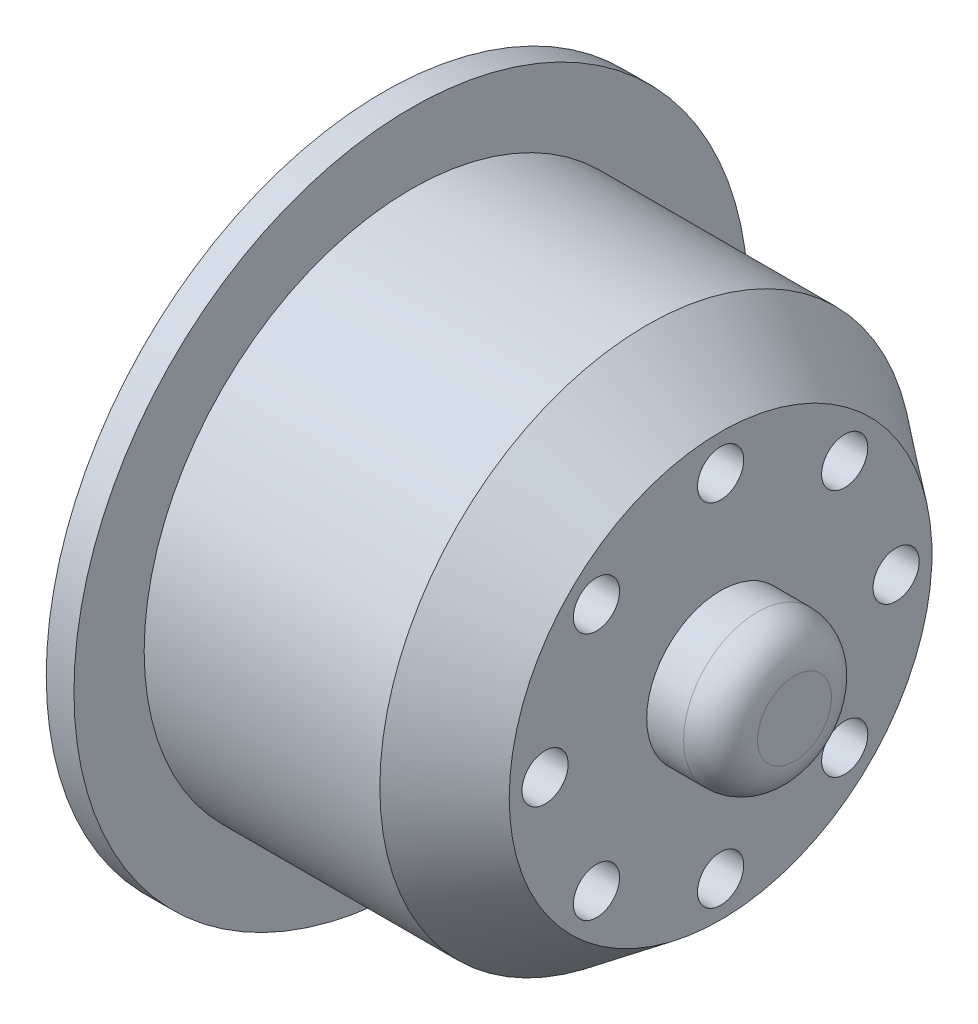
SolidWorks part; units mm, degrees
ref_plane "Front Plane" through (0, 0, 0) normal (0, 0, 1) x (1, 0, 0)
ref_plane "Top Plane" through (0, 0, 0) normal (0, 1, 0) x (1, 0, 0)
ref_plane "Right Plane" through (0, 0, 0) normal (1, 0, 0) x (0, 0, -1)
sketch "Sketch1" plane through (0, 0, 0) normal (0, 1, 0) x (1, 0, 0)
  line L0 (-12.3913, 0) -> (21, 0) construction
  line L1 (-6.1304, 14.45) -> (6.6264, 14.45)
  line L2 (6.6264, 14.45) -> (10.6196, 11.4409)
  line L5 (13.3727, 0) -> (-6.1304, 0)
  line L7 (10.6196, 11.4409) -> (10.6196, 4)
  line L8 (10.6196, 4) -> (14.6196, 4)
  line L9 (14.6196, 4) -> (14.6196, 0)
  line L10 (14.6196, 0) -> (13.3727, 0)
  line L11 (-6.1304, 14.45) -> (-6.1304, 18.25)
  line L12 (-6.1304, 18.25) -> (-7.6304, 18.25)
  line L13 (-7.6304, 18.25) -> (-7.6304, 0)
  line L14 (-7.6304, 0) -> (-6.1304, 0)
  dimension "D1" = 3.9932
  dimension "D2" = 143
  dimension "D3" = 127
  dimension "D4" = 5
  dimension "D5" = 28.9
  dimension "D6" = 16.75
  dimension "D7" = 4
  dimension "D8" = 8
  dimension "D9" = 3.8
  dimension "D10" = 1.5
revolve "Revolve1" add sketch "Sketch1" angle 360 about L0
sketch "Sketch2" plane through (10.6196, 0, 0) normal (1, 0, 0) x (0, 0, -1)
  circle A0 centre (0, 0) radius 9.5 construction
  circle A1 centre (0, 9.5) radius 1.25
  circle A3 centre (6.7175, 6.7175) radius 1.25
  circle A4 centre (9.5, 0) radius 1.25
  circle A5 centre (6.7175, -6.7175) radius 1.25
  circle A6 centre (0, -9.5) radius 1.25
  circle A7 centre (-6.7175, -6.7175) radius 1.25
  circle A8 centre (-9.5, 0) radius 1.25
  circle A9 centre (-6.7175, 6.7175) radius 1.25
  point P22 (0, 0)
  dimension "D1" = 19
  dimension "D2" = 2.5
  dimension "D3" = 8
extrude "Cut-Extrude1" cut sketch "Sketch2" against normal through all
fillet "Fillet1" radius 2 1 edges at (14.6196, 0, 4)
sketch "Sketch3" plane through (-7.6304, 0, 0) normal (-1, 0, 0) x (0, 0, 1)
  circle A0 centre (0, 0) radius 9.5 construction
  circle A1 centre (0, 9.5) radius 2.5
  circle A2 centre (6.7175, 6.7175) radius 2.5
  circle A3 centre (9.5, 0) radius 2.5
  circle A4 centre (6.7175, -6.7175) radius 2.5
  circle A5 centre (0, -9.5) radius 2.5
  circle A6 centre (-6.7175, -6.7175) radius 2.5
  circle A7 centre (-9.5, 0) radius 2.5
  circle A8 centre (-6.7175, 6.7175) radius 2.5
  point P23 (0, 0)
  dimension "D1" = 19
  dimension "D2" = 5
  dimension "D3" = 8
extrude "Cut-Extrude2" cut sketch "Sketch3" against normal offset from surface (13.25 mm away) 5 up to face at (10.6196, 9.5, -1.25)
sketch "Sketch4" plane through (-7.6304, 0, 0) normal (-1, 0, 0) x (0, 0, 1)
  circle A0 centre (0, 0) radius 5.1
  dimension "D1" = 10.2
extrude "Cut-Extrude3" cut sketch "Sketch4" against normal blind 6
